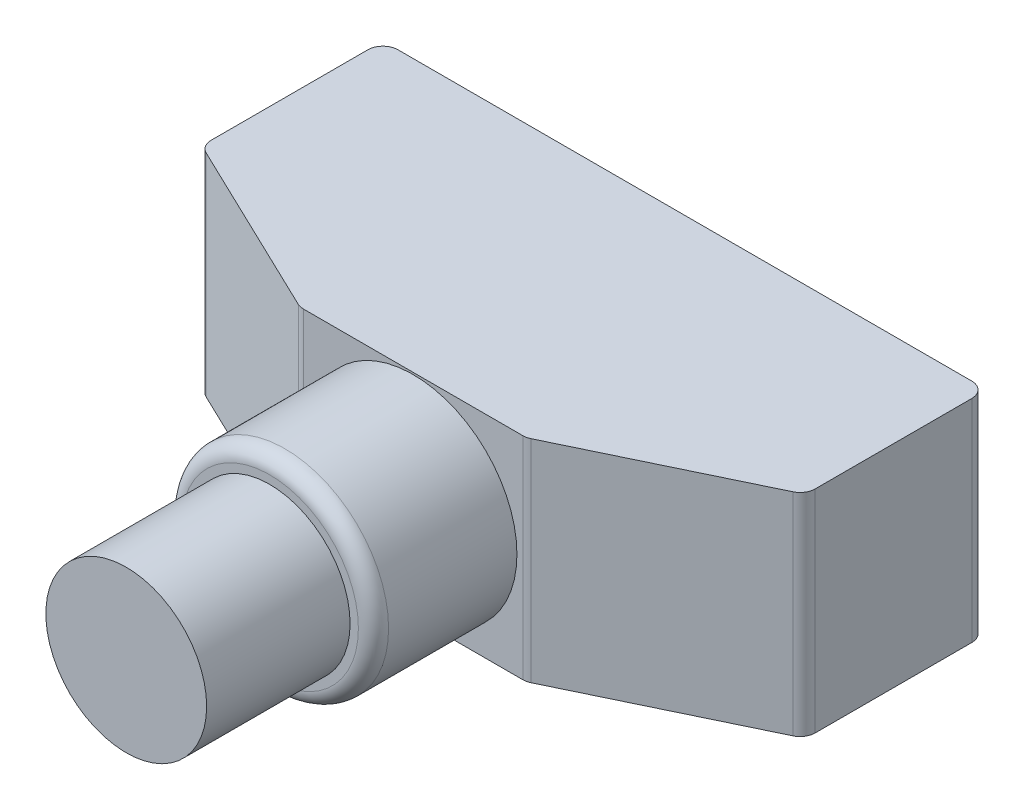
SolidWorks part; units mm, degrees
ref_plane "Front Plane" through (0, 0, 0) normal (0, 0, 1) x (1, 0, 0)
ref_plane "Top Plane" through (0, 0, 0) normal (0, 1, 0) x (1, 0, 0)
ref_plane "Right Plane" through (0, 0, 0) normal (1, 0, 0) x (0, 0, -1)
sketch "Sketch1" plane through (0, 0, 0) normal (0, 1, 0) x (1, 0, 0)
  line L0 (40, 0) -> (40, -12)
  line L1 (0, 0) -> (40, 0)
  line L2 (0, 0) -> (0, -12)
  line L3 (12.5, -18) -> (27.5, -18)
  line L4 (40, 0) -> (40, -12)
  line L5 (40, -12) -> (27.5, -18)
  line L6 (0, -12) -> (12.5, -18)
  point P9 (0, 0)
  dimension "D1" = 40
  dimension "D2" = 18
  dimension "D3" = 12
  dimension "D4" = 12.5
  dimension "D5" = 12.5
extrude "Boss-Extrude1" add sketch "Sketch1" along normal blind 14 contours L2 L6 L3 L5 L0 L1
sketch "Sketch2" plane through (0, 0, 18) normal (0, 0, 1) x (1, 0, 0)
  line L0 (12.5, 14) -> (27.5, 0) construction
  circle A0 centre (20, 7) radius 6.875
  dimension "D1" = 13.75
extrude "Boss-Extrude2" add sketch "Sketch2" along normal blind 9.5
sketch "Sketch3" plane through (0, 0, 27.5) normal (0, 0, 1) x (1, 0, 0)
  line L0 (12.5, 14) -> (27.5, 0) construction
  circle A0 centre (20, 7) radius 5.325
  dimension "D1" = 10.65
extrude "Boss-Extrude3" add sketch "Sketch3" along normal blind 9.5
fillet "Fillet1" radius 1 7 edges at (26.875, 7, 27.5) (0, 7, 0) (40, 7, 0) (40, 7, 12) (27.5, 7, 18) (12.5, 7, 18) (0, 7, 12)
